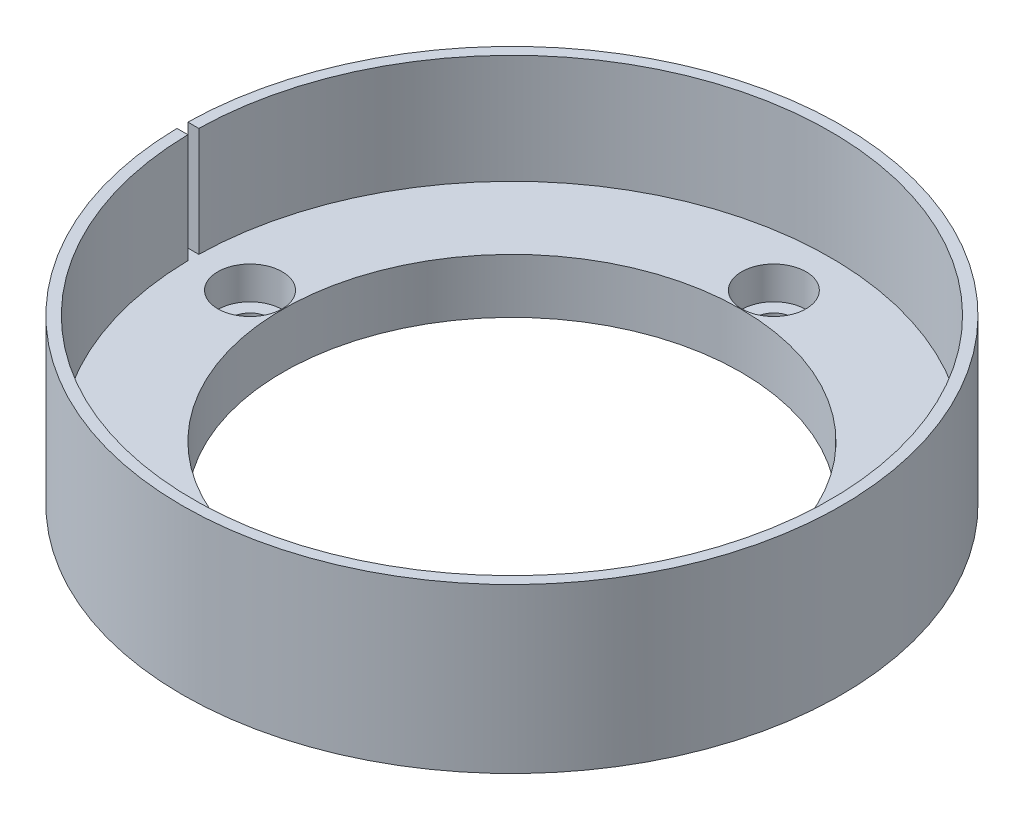
SolidWorks part; units mm, degrees
ref_plane "Alzado" through (0, 0, 0) normal (0, 0, 1) x (1, 0, 0)
ref_plane "Planta" through (0, 0, 0) normal (0, 1, 0) x (1, 0, 0)
ref_plane "Vista lateral" through (0, 0, 0) normal (1, 0, 0) x (0, 0, -1)
sketch "Croquis1" plane through (0, 0, 0) normal (0, 0, 1) x (1, 0, 0)
  line L0 (21, 0) -> (21, 5)
  line L1 (21, 5) -> (29.2, 5)
  line L2 (29.2, 5) -> (29.2, 15)
  line L3 (29.2, 15) -> (30.2, 15)
  line L4 (30.2, 15) -> (30.2, 0)
  line L5 (30.2, 0) -> (21, 0)
  line L6 (0, 26.817) -> (0, -15.2114) construction
  dimension "D1" = 5
  dimension "D2" = 15
  dimension "D3" = 21
  dimension "D4" = 29.2
  dimension "D5" = 30.2
revolve "Revolución1" add sketch "Croquis1" angle 360 about L6
sketch "Croquis2" plane through (0, 5, 0) normal (0, 1, 0) x (1, 0, 0)
  circle A0 centre (0, 0) radius 24 construction
  circle A1 centre (-24, 0) radius 1.7
  circle A2 centre (0, 24) radius 1.7
  circle A3 centre (24, 0) radius 1.7
  circle A4 centre (0, -24) radius 1.7
  dimension "D1" = 48
  dimension "D2" = 3.4
extrude "Cortar-Extruir1" cut sketch "Croquis2" against normal blind 10
sketch "Croquis3" plane through (0, 5, 0) normal (0, 1, 0) x (1, 0, 0)
  circle A0 centre (-24, 0) radius 2.95
  circle A1 centre (0, 24) radius 2.95
  circle A2 centre (24, 0) radius 2.95
  circle A3 centre (0, -24) radius 2.95
  dimension "D1" = 5.9
extrude "Cortar-Extruir2" cut sketch "Croquis3" against normal blind 3
sketch "Croquis4" plane through (0, 15, 0) normal (0, 1, 0) x (1, 0, 0)
  line L1 (-24.2, -0.5) -> (-34.2, -0.5)
  line L2 (-24.2, -0.5) -> (-24.2, 0.5)
  line L3 (-24.2, 0.5) -> (-34.2, 0.5)
  line L4 (-34.2, -0.5) -> (-34.2, 0.5)
  line L5 (-24.2, -0.5) -> (-34.2, 0.5) construction
  line L6 (-24.2, 0.5) -> (-34.2, -0.5) construction
  circle A0 centre (0, 0) radius 29.2 construction
  point P0 (-29.2, 0)
  point P5 (0, 0)
  point P7 (0, 0)
  point P10 (0, 0)
  dimension "D1" = 10
  dimension "D2" = 1
extrude "Cortar-Extruir3" cut sketch "Croquis4" against normal blind 10
